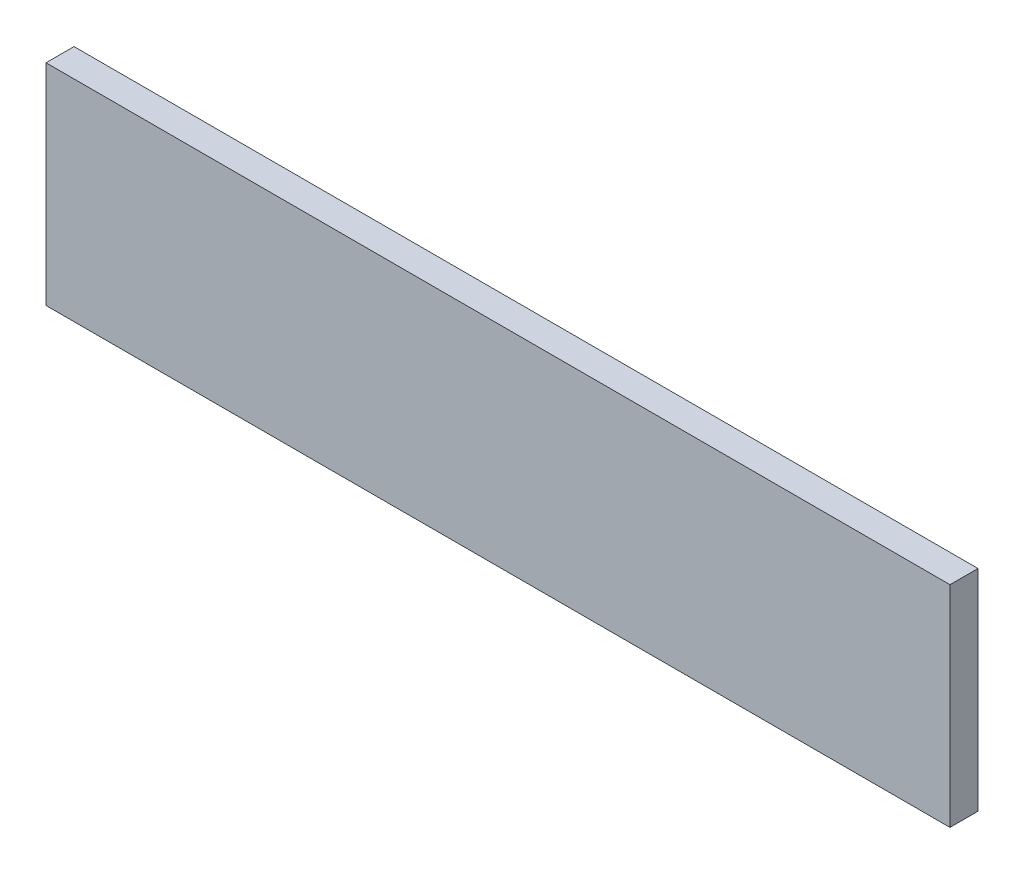
SolidWorks part; units mm, degrees
ref_plane "Alzado" through (0, 0, 0) normal (0, 0, 1) x (1, 0, 0)
ref_plane "Planta" through (0, 0, 0) normal (0, 1, 0) x (1, 0, 0)
ref_plane "Vista lateral" through (0, 0, 0) normal (1, 0, 0) x (0, 0, -1)
sketch "Croquis1" plane through (0, 0, 0) normal (0, 0, 1) x (1, 0, 0)
  line L1 (-417.3965, 139.4794) -> (227.6035, 139.4794)
  line L2 (-417.3965, 139.4794) -> (-417.3965, -10.5206)
  line L3 (-417.3965, -10.5206) -> (227.6035, -10.5206)
  line L4 (227.6035, 139.4794) -> (227.6035, -10.5206)
  dimension "D1" = 645
  dimension "D2" = 150
extrude "Saliente-Extruir1" add sketch "Croquis1" along normal blind 20
